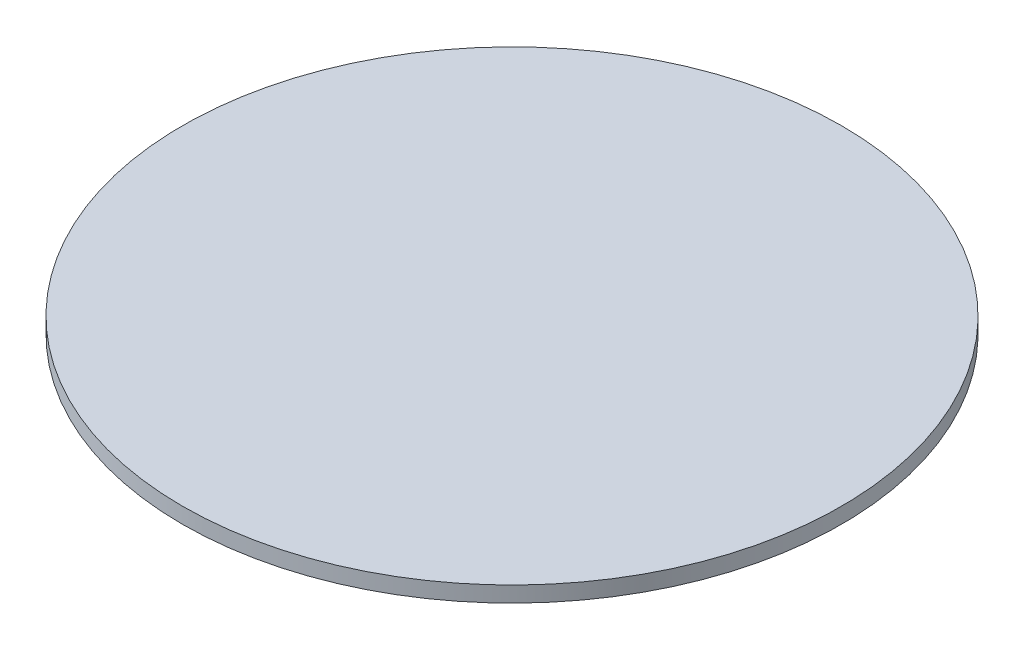
SolidWorks part; units mm, degrees
ref_plane "Plano frontal" through (0, 0, 0) normal (0, 0, 1) x (1, 0, 0)
ref_plane "Plano superior" through (0, 0, 0) normal (0, 1, 0) x (1, 0, 0)
ref_plane "Plano direito" through (0, 0, 0) normal (1, 0, 0) x (0, 0, -1)
sketch "Esboço1" plane through (0, 0, 0) normal (0, 1, 0) x (1, 0, 0)
  circle A0 centre (0, 0) radius 84
extrude "Ressalto-extrusão1" add sketch "Esboço1" along normal blind 4
